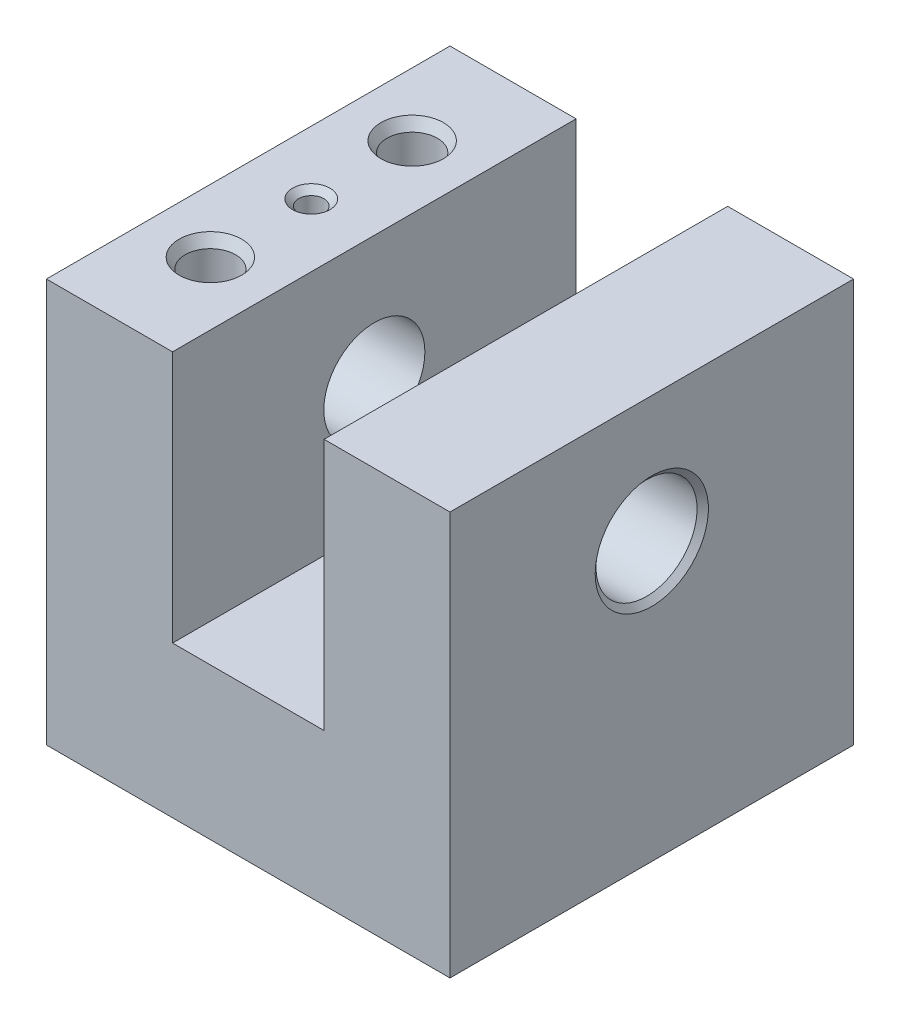
SolidWorks part; units mm, degrees
other "DetailItem1"
other "DetailItem2"
other "DetailItem3"
other "DetailItem4"
material "6061 Alloy"
ref_plane "Front Plane" through (0, 0, 0) normal (0, 0, 1) x (1, 0, 0)
ref_plane "Top Plane" through (0, 0, 0) normal (0, 1, 0) x (1, 0, 0)
ref_plane "Right Plane" through (0, 0, 0) normal (1, 0, 0) x (0, 0, -1)
sketch "Sketch1" plane through (0, 0, 0) normal (0, 0, 1) x (1, 0, 0)
  line L0 (0, 0) -> (50.8, 0)
  line L1 (50.8, 0) -> (50.8, 50.8)
  line L2 (50.8, 50.8) -> (34.9504, 50.8)
  line L3 (34.9504, 50.8) -> (34.9504, 19.05)
  line L4 (34.9504, 19.05) -> (15.875, 19.05)
  line L5 (15.875, 19.05) -> (15.875, 50.8)
  line L6 (15.875, 50.8) -> (0, 50.8)
  line L7 (0, 50.8) -> (0, 0)
  dimension "D1" = 15.875
  dimension "D2" = 19.0754
  dimension "D3" = 50.8
  dimension "D4" = 31.75
  dimension "D6" = 50.8
extrude "Extrude1" add sketch "Sketch1" along normal blind 50.8
sketch "Sketch3" plane through (0, 50.8, 0) normal (0, 1, 0) x (-1, 0, 0)
  line L0 (0, 25.4) -> (-15.875, 25.4) construction
  line L4 (-15.875, 0) -> (0, 0) construction
  line L5 (-15.875, 50.8) -> (-15.875, 0) construction
  circle A0 centre (-7.9375, 25.4) radius 1.5875
  dimension "D1" = 3.175
  dimension "D2" = 7.9375
  dimension "D3" = 25.4
extrude "Cut-Extrude2" cut sketch "Sketch3" against normal blind 7.62
chamfer "Chamfer3" distance 0.762 angle 59 1 edges at (7.9375, 43.18, 26.9875)
chamfer "Chamfer4" distance 0.762 angle 45 1 edges at (7.9375, 50.8, 26.9875)
sketch "Sketch4" plane through (50.8, 0, 0) normal (1, 0, 0) x (0, 0, -1)
  line L0 (-50.8, 50.8) -> (0, 50.8) construction
  line L1 (0, 0) -> (0, 50.8) construction
  circle A0 centre (-25.4, 34.925) radius 6.3627
  dimension "D1" = 12.7254
  dimension "D3" = 25.4
  dimension "D2" = 15.875
extrude "Cut-Extrude3" cut sketch "Sketch4" against normal through all
hole_wizard "1/4-20 Tapped Hole1" positions "3DSketch1" profile "Sketch5" tap size "1/4-20" standard "Ansi Inch"
sketch3d "3DSketch1"
  line L0 (0, 50.8, 50.8) -> (0, 50.8, 0) construction
  line L3 (15.875, 50.8, 50.8) -> (15.875, 50.8, 0) construction
  circle A2 centre (7.9375, 50.8, 25.4) radius 2.3495 construction
  point P0 (7.9375, 50.8, 12.7)
  point P2 (7.9375, 50.8, 38.1)
  point P18 (7.9375, 48.4505, 25.4)
  dimension "D2" = 12.7
  dimension "D1" = 7.9375
  dimension "D3" = 7.9375
  dimension "D4" = 12.7
sketch "Sketch5" plane through (7.9375, 50.8, 12.7) normal (1, 0, 0) x (0, 0, 1)
  line L0 (0, 0) -> (0, 18.0438)
  line L1 (0, 18.0438) -> (2.5527, 16.51)
  line L2 (2.5527, 16.51) -> (2.5527, 12.7)
  line L3 (2.5527, 12.7) -> (3.175, 12.7)
  line L4 (3.175, 12.7) -> (3.175, 0)
  line L5 (3.175, 0) -> (0, 0)
  line L10 (0, 18.0438) -> (-2.5527, 16.51) construction
  line L11 (0, -6.35) -> (0, 107.95) construction
  dimension "Tap Drill Dia." = 5.1054
  dimension "Tap Drill Depth" = 16.51
  dimension "Thread Major Dia." = 6.35
  dimension "Thread Depth" = 12.7
  dimension "Drill Angle" = 118
chamfer "Chamfer6" distance 0.762 angle 60 2 edges at (7.9375, 50.8, 41.275) (7.9375, 50.8, 15.875)
chamfer "Chamfer7" distance 0.762 angle 41 2 edges at (50.8, 41.2877, 25.4) (0, 41.2877, 25.4)
